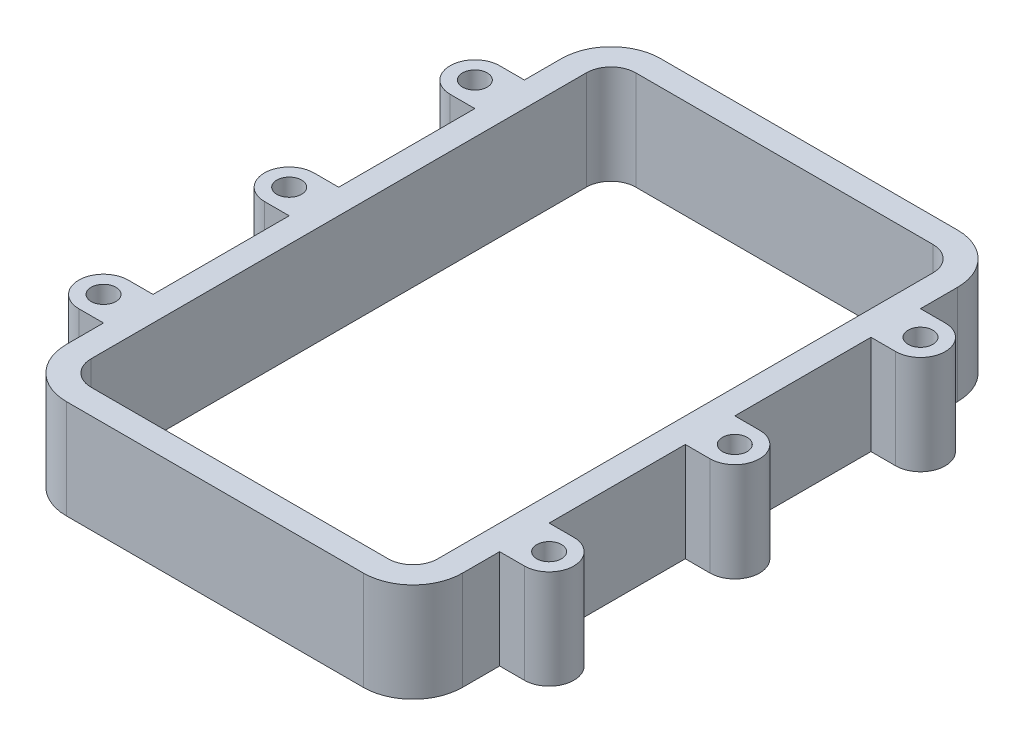
SolidWorks part; units mm, degrees
ref_plane "Alzado" through (0, 0, 0) normal (0, 0, 1) x (1, 0, 0)
ref_plane "Planta" through (0, 0, 0) normal (0, 1, 0) x (1, 0, 0)
ref_plane "Vista lateral" through (0, 0, 0) normal (1, 0, 0) x (0, 0, -1)
sketch "Sketch1" plane through (0, 0, 0) normal (0, 1, 0) x (1, 0, 0)
  line L0 (0, 0) -> (0, 85.9475) construction
  line L1 (0, 0) -> (77.9076, 0) construction
  line L2 (0, 76.2) -> (38.1, 76.2)
  line L3 (50.8, 63.5) -> (50.8, 53.975)
  line L4 (38.1, -76.2) -> (-4.319, -76.2)
  line L5 (0, 69.85) -> (38.1, 69.85)
  line L6 (44.45, 63.5) -> (44.45, -63.5)
  line L7 (38.1, -69.85) -> (-4.319, -69.85)
  line L8 (-38.1, -69.85) -> (-4.319, -69.85)
  line L9 (-38.1, -76.2) -> (-4.319, -76.2)
  line L10 (0, 69.85) -> (-38.1, 69.85)
  line L11 (0, 76.2) -> (-38.1, 76.2)
  line L12 (-44.45, 63.5) -> (-44.45, -63.5)
  line L13 (-50.8, 63.5) -> (-50.8, 53.975)
  line L14 (57.15, 53.975) -> (50.8, 53.975)
  line L15 (57.15, 41.275) -> (50.8, 41.275)
  line L16 (50.8, 41.275) -> (50.8, 6.35)
  line L17 (50.8, 63.5) -> (50.8, -63.5) construction
  line L18 (57.15, -6.35) -> (50.8, -6.35)
  line L19 (57.15, 6.35) -> (50.8, 6.35)
  line L20 (57.15, -53.975) -> (50.8, -53.975)
  line L21 (57.15, -41.275) -> (50.8, -41.275)
  line L22 (-57.15, -41.275) -> (-50.8, -41.275)
  line L23 (-57.15, -53.975) -> (-50.8, -53.975)
  line L24 (-57.15, 41.275) -> (-50.8, 41.275)
  line L25 (-57.15, 53.975) -> (-50.8, 53.975)
  line L26 (-57.15, -6.35) -> (-50.8, -6.35)
  line L27 (-57.15, 6.35) -> (-50.8, 6.35)
  line L28 (50.8, -6.35) -> (50.8, -41.275)
  line L29 (50.8, -53.975) -> (50.8, -63.5)
  line L30 (-50.8, -53.975) -> (-50.8, -63.5)
  line L31 (-50.8, -6.35) -> (-50.8, -41.275)
  line L32 (-50.8, 41.275) -> (-50.8, 6.35)
  arc A0 (50.8, -63.5) -> (38.1, -76.2) centre (38.1, -63.5) cw
  arc A1 (38.1, 76.2) -> (50.8, 63.5) centre (38.1, 63.5) cw
  arc A2 (38.1, 69.85) -> (44.45, 63.5) centre (38.1, 63.5) cw
  arc A3 (44.45, -63.5) -> (38.1, -69.85) centre (38.1, -63.5) cw
  arc A4 (-44.45, -63.5) -> (-38.1, -69.85) centre (-38.1, -63.5) ccw
  arc A5 (-50.8, -63.5) -> (-38.1, -76.2) centre (-38.1, -63.5) ccw
  arc A6 (-38.1, 69.85) -> (-44.45, 63.5) centre (-38.1, 63.5) ccw
  arc A7 (-38.1, 76.2) -> (-50.8, 63.5) centre (-38.1, 63.5) ccw
  circle A8 centre (57.15, 47.625) radius 3.175
  arc A9 (57.15, 41.275) -> (57.15, 53.975) centre (57.15, 47.625) ccw
  arc A10 (57.15, -6.35) -> (57.15, 6.35) centre (57.15, 0) ccw
  circle A11 centre (57.15, 0) radius 3.175
  arc A12 (57.15, -53.975) -> (57.15, -41.275) centre (57.15, -47.625) ccw
  circle A13 centre (57.15, -47.625) radius 3.175
  circle A14 centre (-57.15, -47.625) radius 3.175
  arc A15 (-57.15, -53.975) -> (-57.15, -41.275) centre (-57.15, -47.625) cw
  circle A16 centre (-57.15, 47.625) radius 3.175
  arc A17 (-57.15, 41.275) -> (-57.15, 53.975) centre (-57.15, 47.625) cw
  circle A18 centre (-57.15, 0) radius 3.175
  arc A19 (-57.15, -6.35) -> (-57.15, 6.35) centre (-57.15, 0) cw
  point P68 (0, 0)
  point P69 (0, 0)
  point P70 (0, 0)
  point P71 (77.9076, 0)
  point P72 (0, 85.9475)
  dimension "D3" = 12.7
  dimension "D8" = 6.35
  dimension "D9" = 12.7
  dimension "D1" = 76.2
  dimension "D2" = 152.4
  dimension "D4" = 50.8
  dimension "D6" = 28.575
  dimension "D7" = 12.7
  dimension "D11" = 76.2
  dimension "D5" = 6.35
  dimension "D10" = 3
extrude "Boss-Extrude1" add sketch "Sketch1" along normal blind 25.4
